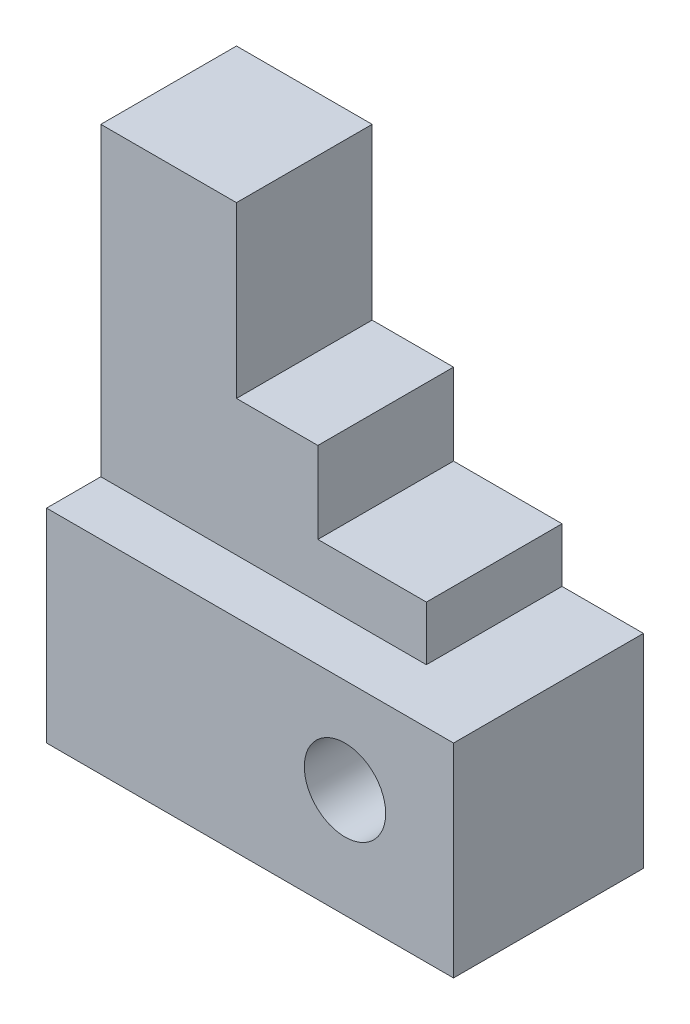
SolidWorks part; units mm, degrees
material "Aluminum Bronze"
ref_plane "Front Plane" through (0, 0, 0) normal (0, 0, 1) x (1, 0, 0)
ref_plane "Top Plane" through (0, 0, 0) normal (0, 1, 0) x (1, 0, 0)
ref_plane "Right Plane" through (0, 0, 0) normal (1, 0, 0) x (0, 0, -1)
sketch "Sketch1" plane through (0, 0, 0) normal (0, 1, 0) x (1, 0, 0)
  line L1 (0, 0) -> (60, 0)
  line L2 (0, 0) -> (0, 28)
  line L3 (0, 28) -> (60, 28)
  line L4 (60, 0) -> (60, 28)
  dimension "D1" = 60
  dimension "D2" = 28
extrude "Boss-Extrude1" add sketch "Sketch1" along normal blind 30
sketch "Sketch3" plane through (0, 0, -28) normal (0, 0, -1) x (-1, 0, 0)
  line L0 (0, 30) -> (0, 75)
  line L1 (0, 75) -> (-20, 75)
  line L2 (-20, 75) -> (-20, 50)
  line L3 (-20, 50) -> (-32, 50)
  line L4 (-32, 50) -> (-32, 38)
  line L5 (-32, 38) -> (-48, 38)
  line L6 (-48, 38) -> (-48, 30)
  line L7 (-60, 30) -> (0, 30) construction
  line L8 (-48, 30) -> (0, 30)
  dimension "D1" = 20
  dimension "D2" = 12
  dimension "D3" = 12
  dimension "D4" = 12
  dimension "D5" = 75
  dimension "D6" = 20
extrude "Boss-Extrude3" add sketch "Sketch3" against normal blind 20
sketch "Sketch4" plane through (0, 0, 0) normal (0, 0, 1) x (1, 0, 0)
  line L0 (0, 0) -> (60, 0) construction
  line L1 (60, 30) -> (60, 0) construction
  circle A0 centre (44, 16) radius 6
  dimension "D3" = 12
  dimension "D1" = 16
  dimension "D2" = 16
extrude "Cut-Extrude1" cut sketch "Sketch4" against normal through all
